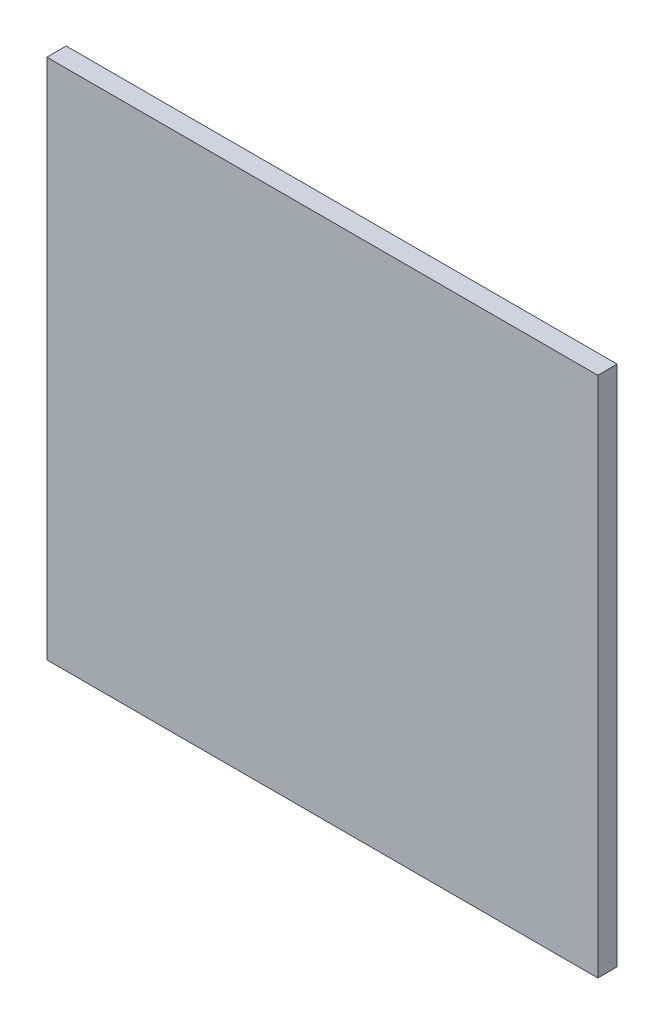
SolidWorks part; units mm, degrees
material "Acrylic (Medium-high impact)"
ref_plane "Front Plane" through (0, 0, 0) normal (0, 0, 1) x (1, 0, 0)
ref_plane "Top Plane" through (0, 0, 0) normal (0, 1, 0) x (1, 0, 0)
ref_plane "Right Plane" through (0, 0, 0) normal (1, 0, 0) x (0, 0, -1)
sketch "Sketch1" plane through (0, 0, 0) normal (0, 0, 1) x (1, 0, 0)
  line L1 (-45.2438, 42.8625) -> (45.2437, 42.8625)
  line L2 (-45.2438, 42.8625) -> (-45.2438, -42.8625)
  line L3 (-45.2438, -42.8625) -> (45.2437, -42.8625)
  line L4 (45.2437, 42.8625) -> (45.2437, -42.8625)
  line L5 (-45.2438, 42.8625) -> (45.2437, -42.8625) construction
  line L6 (-45.2438, -42.8625) -> (45.2437, 42.8625) construction
  point P0 (0, 0)
  dimension "D1" = 85.725
  dimension "D2" = 90.4875
extrude "Boss-Extrude1" add sketch "Sketch1" along normal blind 3.175
